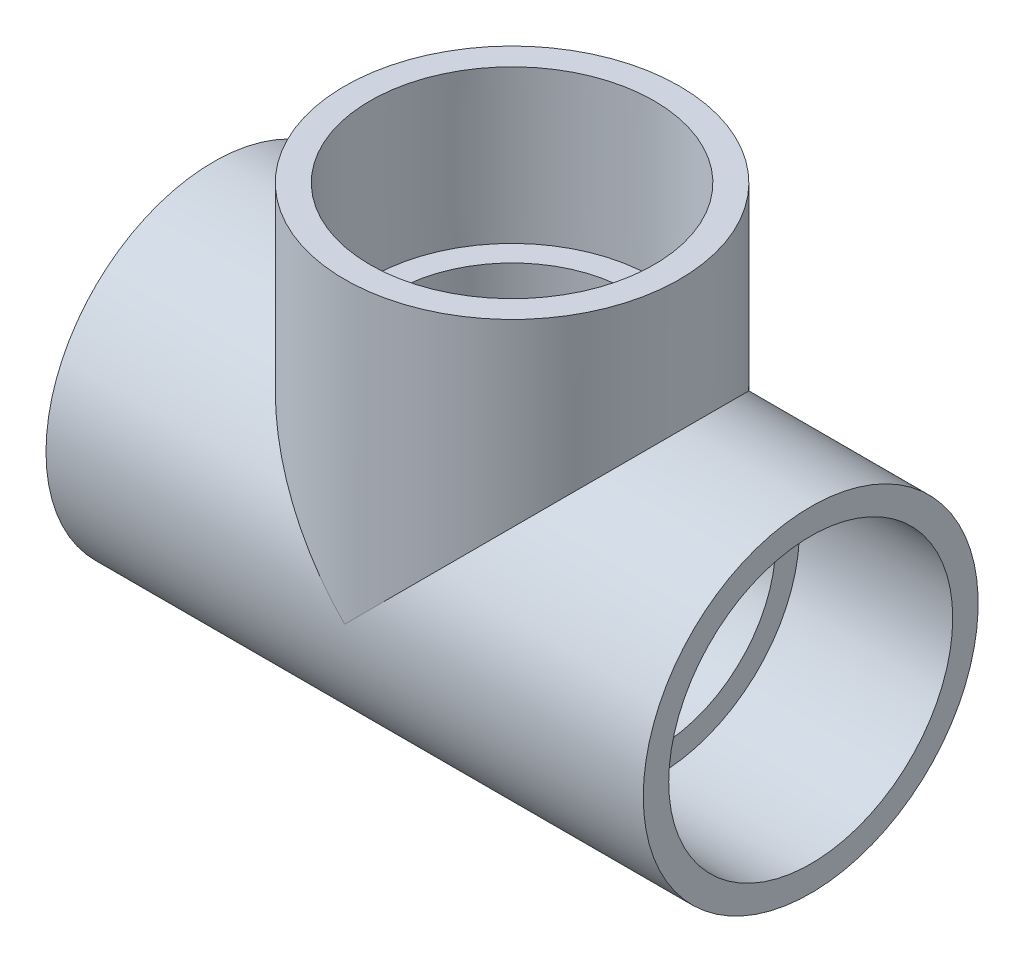
SolidWorks part; units mm, degrees
ref_plane "Front Plane" through (0, 0, 0) normal (0, 0, 1) x (1, 0, 0)
ref_plane "Top Plane" through (0, 0, 0) normal (0, 1, 0) x (1, 0, 0)
ref_plane "Right Plane" through (0, 0, 0) normal (1, 0, 0) x (0, 0, -1)
sketch "Sketch0" plane through (0, 0, 0) normal (0, 0, 1) x (1, 0, 0)
  line L0 (-93.9038, 0) -> (0, 0) construction
  line L1 (0, 0) -> (0, 93.9038) construction
  line L2 (-46.0248, 0) -> (0, 0) construction
  line L3 (0, 0) -> (0, 46.0248) construction
  line L4 (-93.9038, 52.6542) -> (-93.9038, -52.6542) construction
  line L5 (-46.0248, 44.3484) -> (-93.9038, 44.6532) construction
  line L6 (-46.0248, 44.3484) -> (-46.0248, -44.3484) construction
  line L7 (-46.0248, -44.3484) -> (-93.9038, -44.6532) construction
  line L8 (-93.9038, 44.6532) -> (-93.9038, -44.6532) construction
  line L9 (-52.6542, 93.9038) -> (52.6542, 93.9038) construction
  line L10 (-44.6532, 93.9038) -> (44.6532, 93.9038) construction
  line L11 (44.6532, 93.9038) -> (44.3484, 46.0248) construction
  line L12 (44.3484, 46.0248) -> (-44.3484, 46.0248) construction
  line L13 (-44.3484, 46.0248) -> (-44.6532, 93.9038) construction
  line L14 (-46.0248, 36.83) -> (-46.0248, -36.83) construction
  line L18 (-36.83, 46.0248) -> (36.83, 46.0248) construction
  dimension "H" = 93.9038
  dimension "G" = 46.0248
  dimension "M" = 105.3084
  dimension "OD A" = 89.3064
  dimension "OD B" = 88.6968
  dimension "ID" = 73.66
sketch "Sketch1" plane through (0, 0, 0) normal (0, 0, 1) x (1, 0, 0)
  line L0 (-93.9038, 0) -> (0, 0) construction
  line L1 (-93.9038, 0) -> (0, 0) construction
  line L3 (-93.9038, -52.6542) -> (-46.0248, -52.6542)
  line L4 (-93.9038, -52.6542) -> (-93.9038, -44.6532)
  line L5 (-93.9038, -44.6532) -> (-46.0248, -44.3484)
  line L6 (-46.0248, -52.6542) -> (-46.0248, -44.3484)
revolve "Revolve1" add sketch "Sketch1" angle 360 about L1
mirror "Mirror1" about plane through (0, 0, 0) normal (1, 0, 0) of bodies 102
sketch "Sketch2" plane through (0, 0, 0) normal (0, 0, 1) x (1, 0, 0)
  line L0 (44.6532, 93.9038) -> (44.3484, 46.0248)
  line L1 (44.3484, 46.0248) -> (52.6542, 46.0248)
  line L2 (52.6542, 46.0248) -> (52.6542, 93.9038)
  line L3 (52.6542, 93.9038) -> (44.6532, 93.9038)
  line L4 (0, 0) -> (0, 93.9038) construction
  line L5 (0, 0) -> (0, 93.9038) construction
revolve "Revolve2" add sketch "Sketch2" angle 360 about L5
sketch "Sketch3" plane through (-46.0248, 0, 0) normal (1, 0, 0) x (0, 0, -1)
  line L0 (-52.6542, 46.0248) -> (52.6542, 46.0248) construction
  line L2 (25.577, 46.0248) -> (-25.577, 46.0248)
  circle A1 centre (0, 0) radius 52.6542 construction
  arc A3 (-25.577, 46.0248) -> (25.577, 46.0248) centre (0, 0) ccw
extrude "Boss-Extrude1" add sketch "Sketch3" along normal up to surface (92.0496 mm away) up to face at (46.0248, 0, 44.3484)
sketch "Sketch4" plane through (0, 46.0248, 0) normal (0, -1, 0) x (1, 0, 0)
  line L0 (46.0248, -25.577) -> (46.0248, 25.577)
  line L1 (-46.0248, -25.577) -> (-46.0248, 25.577)
  circle A0 centre (0, 0) radius 52.6542 construction
  arc A1 (46.0248, 25.577) -> (-46.0248, 25.577) centre (0, 0) ccw
  arc A2 (-46.0248, -25.577) -> (46.0248, -25.577) centre (0, 0) ccw
  circle A3 centre (0, 0) radius 52.6542 construction
  circle A4 centre (0, 0) radius 52.6542 construction
extrude "Boss-Extrude2" add sketch "Sketch4" along normal up to surface (46.0248 mm away)
sketch "Sketch5" plane through (-46.0248, 0, 0) normal (-1, 0, 0) x (0, 0, 1)
  line L0 (0, 44.3484) -> (0, -44.3484) construction
  circle A0 centre (0, 0) radius 36.83
extrude "Cut-Extrude1" cut sketch "Sketch5" against normal up to surface (92.0496 mm away) up to face at (46.0248, 0, 44.3484)
sketch "Sketch6" plane through (0, 46.0248, 0) normal (0, 1, 0) x (1, 0, 0)
  circle A0 centre (0, 0) radius 36.83
extrude "Cut-Extrude2" cut sketch "Sketch6" against normal up to vertex
